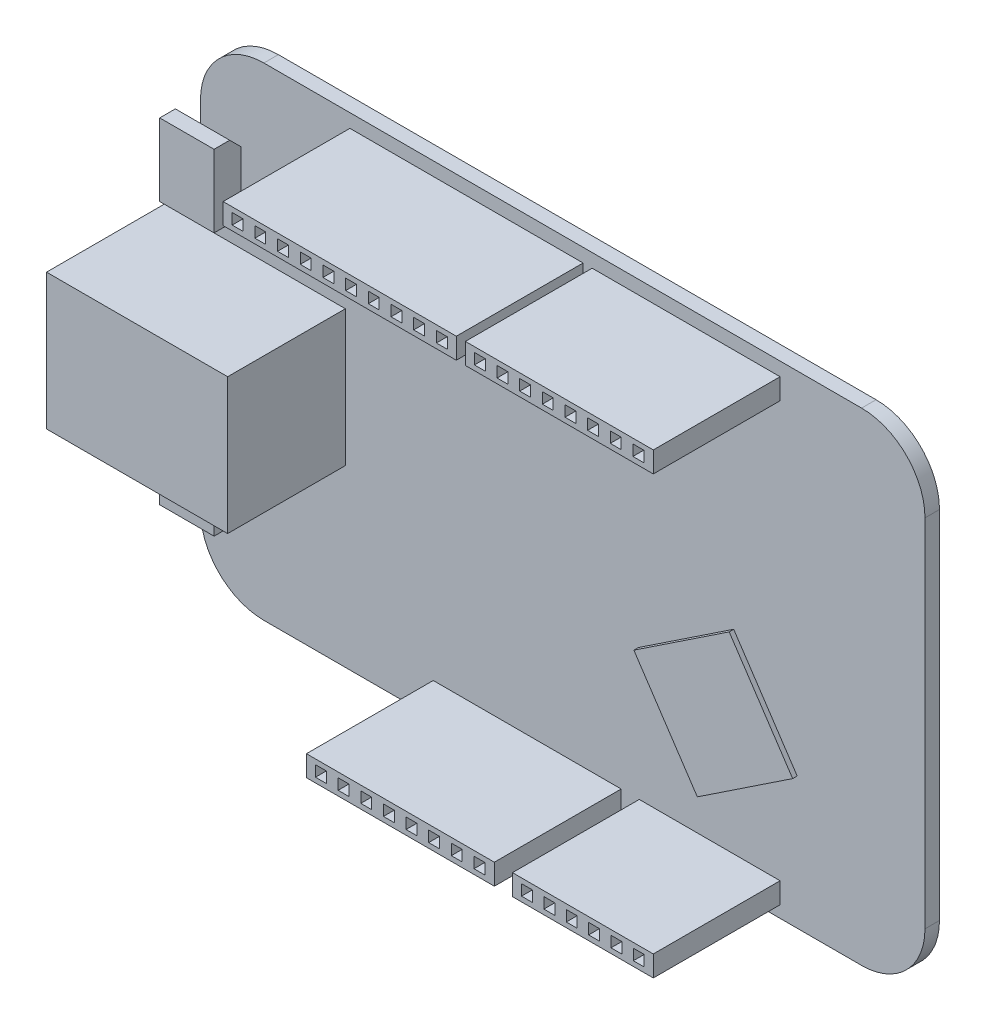
SolidWorks part; units mm, degrees
other "Camera1"
ref_plane "Plan de face" through (0, 0, 0) normal (0, 0, 1) x (1, 0, 0)
ref_plane "Plan de dessus" through (0, 0, 0) normal (0, 1, 0) x (1, 0, 0)
ref_plane "Plan de droite" through (0, 0, 0) normal (1, 0, 0) x (0, 0, -1)
sketch "Esquisse1" plane through (0, 0, 0) normal (0, 0, 1) x (1, 0, 0)
  line L0 (0, 0) -> (0, 53.3)
  line L1 (0, 53.3) -> (80, 53.3)
  line L2 (80, 53.3) -> (80, 0)
  line L6 (80, 0) -> (0, 0)
  dimension "D1" = 53.3
  dimension "D2" = 80
extrude "Boss.-Extru.1" add sketch "Esquisse1" along normal blind 1.6
sketch "Esquisse4" plane through (0, 0, 1.6) normal (0, 0, 1) x (1, 0, 0)
  line L0 (0, 0) -> (80, 0) construction
  line L1 (64, 3.6) -> (48.45, 3.6)
  line L2 (64, 3.6) -> (64, 1.3)
  line L3 (64, 1.3) -> (48.45, 1.3)
  line L4 (48.45, 3.6) -> (48.45, 1.3)
  line L5 (49.45, 3.05) -> (50.65, 3.05)
  line L6 (49.45, 3.05) -> (49.45, 1.85)
  line L7 (49.45, 1.85) -> (50.65, 1.85)
  line L8 (50.65, 3.05) -> (50.65, 1.85)
  line L10 (51.92, 1.85) -> (53.12, 1.85)
  line L11 (53.12, 3.05) -> (53.12, 1.85)
  line L12 (51.92, 3.05) -> (53.12, 3.05)
  line L13 (51.92, 3.05) -> (51.92, 1.85)
  line L14 (54.39, 1.85) -> (55.59, 1.85)
  line L15 (55.59, 3.05) -> (55.59, 1.85)
  line L16 (54.39, 3.05) -> (55.59, 3.05)
  line L17 (54.39, 3.05) -> (54.39, 1.85)
  line L18 (56.86, 1.85) -> (58.06, 1.85)
  line L19 (58.06, 3.05) -> (58.06, 1.85)
  line L20 (56.86, 3.05) -> (58.06, 3.05)
  line L21 (56.86, 3.05) -> (56.86, 1.85)
  line L22 (59.33, 1.85) -> (60.53, 1.85)
  line L23 (60.53, 3.05) -> (60.53, 1.85)
  line L24 (59.33, 3.05) -> (60.53, 3.05)
  line L25 (59.33, 3.05) -> (59.33, 1.85)
  line L26 (61.8, 1.85) -> (63, 1.85)
  line L27 (63, 3.05) -> (63, 1.85)
  line L28 (61.8, 3.05) -> (63, 3.05)
  line L29 (61.8, 3.05) -> (61.8, 1.85)
  line L30 (80, 0) -> (80, 53.3) construction
  dimension "D1" = 1
  dimension "D2" = 2.3
  dimension "D3" = 1.3
  dimension "D4" = 16
  dimension "D5" = 1.2
  dimension "D6" = 0.55
  dimension "D7" = 1
  dimension "D9" = 15.55
  dimension "D8" = 6
extrude "Boss.-Extru.4" add sketch "Esquisse4" along normal blind 14 separate body
sketch "Esquisse8" plane through (0, 0, 1.6) normal (0, 0, 1) x (1, 0, 0)
  line L0 (64, 3.6) -> (48.45, 3.6) construction
  line L1 (46.45, 3.6) -> (25.7, 3.6)
  line L2 (46.45, 3.6) -> (46.45, 1.3)
  line L3 (46.45, 1.3) -> (25.7, 1.3)
  line L4 (25.7, 3.6) -> (25.7, 1.3)
  line L5 (48.45, 1.3) -> (64, 1.3) construction
  line L6 (48.45, 3.6) -> (48.45, 1.3) construction
  line L7 (50.65, 3.05) -> (49.45, 3.05) construction
  line L8 (26.7, 3.05) -> (27.9, 3.05)
  line L9 (26.7, 3.05) -> (26.7, 1.85)
  line L10 (26.7, 1.85) -> (27.9, 1.85)
  line L11 (27.9, 3.05) -> (27.9, 1.85)
  line L12 (49.45, 1.85) -> (50.65, 1.85) construction
  line L13 (29.2, 1.85) -> (30.4, 1.85)
  line L14 (30.4, 3.05) -> (30.4, 1.85)
  line L15 (29.2, 3.05) -> (30.4, 3.05)
  line L16 (29.2, 3.05) -> (29.2, 1.85)
  line L17 (31.7, 1.85) -> (32.9, 1.85)
  line L18 (32.9, 3.05) -> (32.9, 1.85)
  line L19 (31.7, 3.05) -> (32.9, 3.05)
  line L20 (31.7, 3.05) -> (31.7, 1.85)
  line L21 (34.2, 1.85) -> (35.4, 1.85)
  line L22 (35.4, 3.05) -> (35.4, 1.85)
  line L23 (34.2, 3.05) -> (35.4, 3.05)
  line L24 (34.2, 3.05) -> (34.2, 1.85)
  line L25 (36.7, 1.85) -> (37.9, 1.85)
  line L26 (37.9, 3.05) -> (37.9, 1.85)
  line L27 (36.7, 3.05) -> (37.9, 3.05)
  line L28 (36.7, 3.05) -> (36.7, 1.85)
  line L29 (39.2, 1.85) -> (40.4, 1.85)
  line L30 (40.4, 3.05) -> (40.4, 1.85)
  line L31 (39.2, 3.05) -> (40.4, 3.05)
  line L32 (39.2, 3.05) -> (39.2, 1.85)
  line L33 (41.7, 1.85) -> (42.9, 1.85)
  line L34 (42.9, 3.05) -> (42.9, 1.85)
  line L35 (41.7, 3.05) -> (42.9, 3.05)
  line L36 (41.7, 3.05) -> (41.7, 1.85)
  line L37 (44.2, 1.85) -> (45.4, 1.85)
  line L38 (45.4, 3.05) -> (45.4, 1.85)
  line L39 (44.2, 3.05) -> (45.4, 3.05)
  line L40 (44.2, 3.05) -> (44.2, 1.85)
  point P8 (48.45, 2.45)
  dimension "D1" = 2
  dimension "D2" = 20.75
  dimension "D3" = 1.2
  dimension "D4" = 1
  dimension "D5" = 8
extrude "Boss.-Extru.6" add sketch "Esquisse8" along normal blind 14 separate body
sketch "Esquisse19" plane through (0, 0, 1.6) normal (0, 0, 1) x (1, 0, 0)
  line L0 (64, 51.8) -> (43.25, 51.8)
  line L1 (64, 51.8) -> (64, 49.5)
  line L2 (64, 49.5) -> (43.25, 49.5)
  line L3 (43.25, 51.8) -> (43.25, 49.5)
  line L4 (44.25, 51.25) -> (45.45, 51.25)
  line L5 (44.25, 51.25) -> (44.25, 50.05)
  line L6 (44.25, 50.05) -> (45.45, 50.05)
  line L7 (45.45, 51.25) -> (45.45, 50.05)
  line L8 (46.75, 50.05) -> (47.95, 50.05)
  line L9 (47.95, 51.25) -> (47.95, 50.05)
  line L10 (46.75, 51.25) -> (47.95, 51.25)
  line L11 (46.75, 51.25) -> (46.75, 50.05)
  line L12 (49.25, 50.05) -> (50.45, 50.05)
  line L13 (50.45, 51.25) -> (50.45, 50.05)
  line L14 (49.25, 51.25) -> (50.45, 51.25)
  line L15 (49.25, 51.25) -> (49.25, 50.05)
  line L16 (51.75, 50.05) -> (52.95, 50.05)
  line L17 (52.95, 51.25) -> (52.95, 50.05)
  line L18 (51.75, 51.25) -> (52.95, 51.25)
  line L19 (51.75, 51.25) -> (51.75, 50.05)
  line L20 (54.25, 50.05) -> (55.45, 50.05)
  line L21 (55.45, 51.25) -> (55.45, 50.05)
  line L22 (54.25, 51.25) -> (55.45, 51.25)
  line L23 (54.25, 51.25) -> (54.25, 50.05)
  line L24 (56.75, 50.05) -> (57.95, 50.05)
  line L25 (57.95, 51.25) -> (57.95, 50.05)
  line L26 (56.75, 51.25) -> (57.95, 51.25)
  line L27 (56.75, 51.25) -> (56.75, 50.05)
  line L28 (59.25, 50.05) -> (60.45, 50.05)
  line L29 (60.45, 51.25) -> (60.45, 50.05)
  line L30 (59.25, 51.25) -> (60.45, 51.25)
  line L31 (59.25, 51.25) -> (59.25, 50.05)
  line L32 (61.75, 50.05) -> (62.95, 50.05)
  line L33 (62.95, 51.25) -> (62.95, 50.05)
  line L34 (61.75, 51.25) -> (62.95, 51.25)
  line L35 (61.75, 51.25) -> (61.75, 50.05)
  line L36 (80, 0) -> (80, 53.3) construction
  line L38 (80, 53.3) -> (0, 53.3) construction
  dimension "D1" = 20.75
  dimension "D2" = 1.2
  dimension "D3" = 1
  dimension "D4" = 2.3
  dimension "D5" = 0.55
  dimension "D6" = 0.55
  dimension "D7" = 1.2
  dimension "D8" = 1.3
  dimension "D9" = 1.3
  dimension "D10" = 1.3
  dimension "D11" = 1.3
  dimension "D12" = 1.3
  dimension "D13" = 1.3
  dimension "D14" = 1.3
  dimension "D15" = 1.05
  dimension "D16" = 1.2
  dimension "D17" = 1.2
  dimension "D18" = 1.2
  dimension "D19" = 1.2
  dimension "D20" = 1.2
  dimension "D21" = 1.2
  dimension "D22" = 16
  dimension "D23" = 1.5
extrude "Boss.-Extru.15" add sketch "Esquisse19" along normal blind 14 separate body
sketch "Esquisse20" plane through (0, 0, 1.6) normal (0, 0, 1) x (1, 0, 0)
  line L0 (43.25, 49.5) -> (64, 49.5) construction
  line L1 (42.25, 49.5) -> (16.5, 49.5)
  line L2 (42.25, 49.5) -> (42.25, 51.8)
  line L3 (42.25, 51.8) -> (16.5, 51.8)
  line L4 (16.5, 49.5) -> (16.5, 51.8)
  line L5 (64, 51.8) -> (43.25, 51.8) construction
  line L6 (43.25, 51.8) -> (43.25, 49.5) construction
  line L7 (45.45, 51.25) -> (44.25, 51.25) construction
  line L8 (41.25, 50.05) -> (40.05, 50.05)
  line L9 (41.25, 50.05) -> (41.25, 51.25)
  line L10 (41.25, 51.25) -> (40.05, 51.25)
  line L11 (40.05, 50.05) -> (40.05, 51.25)
  line L12 (44.25, 50.05) -> (45.45, 50.05) construction
  line L13 (38.7444, 50.05) -> (37.5444, 50.05)
  line L14 (37.5444, 50.05) -> (37.5444, 51.25)
  line L15 (38.7444, 51.25) -> (37.5444, 51.25)
  line L16 (38.7444, 50.05) -> (38.7444, 51.25)
  line L17 (36.2389, 50.05) -> (35.0389, 50.05)
  line L18 (35.0389, 50.05) -> (35.0389, 51.25)
  line L19 (36.2389, 51.25) -> (35.0389, 51.25)
  line L20 (36.2389, 50.05) -> (36.2389, 51.25)
  line L21 (33.7333, 50.05) -> (32.5333, 50.05)
  line L22 (32.5333, 50.05) -> (32.5333, 51.25)
  line L23 (33.7333, 51.25) -> (32.5333, 51.25)
  line L24 (33.7333, 50.05) -> (33.7333, 51.25)
  line L25 (31.2278, 50.05) -> (30.0278, 50.05)
  line L26 (30.0278, 50.05) -> (30.0278, 51.25)
  line L27 (31.2278, 51.25) -> (30.0278, 51.25)
  line L28 (31.2278, 50.05) -> (31.2278, 51.25)
  line L29 (28.7222, 50.05) -> (27.5222, 50.05)
  line L30 (27.5222, 50.05) -> (27.5222, 51.25)
  line L31 (28.7222, 51.25) -> (27.5222, 51.25)
  line L32 (28.7222, 50.05) -> (28.7222, 51.25)
  line L33 (26.2167, 50.05) -> (25.0167, 50.05)
  line L34 (25.0167, 50.05) -> (25.0167, 51.25)
  line L35 (26.2167, 51.25) -> (25.0167, 51.25)
  line L36 (26.2167, 50.05) -> (26.2167, 51.25)
  line L37 (23.7111, 50.05) -> (22.5111, 50.05)
  line L38 (22.5111, 50.05) -> (22.5111, 51.25)
  line L39 (23.7111, 51.25) -> (22.5111, 51.25)
  line L40 (23.7111, 50.05) -> (23.7111, 51.25)
  line L41 (21.2056, 50.05) -> (20.0056, 50.05)
  line L42 (20.0056, 50.05) -> (20.0056, 51.25)
  line L43 (21.2056, 51.25) -> (20.0056, 51.25)
  line L44 (21.2056, 50.05) -> (21.2056, 51.25)
  line L45 (18.7, 50.05) -> (17.5, 50.05)
  line L46 (17.5, 50.05) -> (17.5, 51.25)
  line L47 (18.7, 51.25) -> (17.5, 51.25)
  line L48 (18.7, 50.05) -> (18.7, 51.25)
  dimension "D1" = 25.75
  dimension "D2" = 1
  dimension "D3" = 1.2
  dimension "D4" = 1
  dimension "D6" = 1
  dimension "D5" = 10
extrude "Boss.-Extru.16" add sketch "Esquisse20" along normal blind 14 separate body
fillet "Fillet1" radius 7 4 edges at (80, 53.3, 0.8) (80, 0, 0.8) (0, 0, 0.8) (0, 53.3, 0.8)
sketch "Sketch1" plane through (0, 0, 1.6) normal (0, 0, 1) x (1, 0, 0)
  line L0 (55.3626, 7.5515) -> (65.8884, 14.561)
  line L1 (65.8884, 14.561) -> (58.8788, 25.0868)
  line L2 (58.8788, 25.0868) -> (48.353, 18.0772)
  line L3 (48.353, 18.0772) -> (55.3626, 7.5515)
extrude "Boss-Extrude1" add sketch "Sketch1" along normal blind 0.5
sketch "Sketch2" plane through (0, 0, 1.6) normal (0, 0, 1) x (1, 0, 0)
  line L0 (73, 53.3) -> (7, 53.3) construction
  line L1 (-4, 19.3) -> (16, 19.3)
  line L2 (-4, 19.3) -> (-4, 34.3)
  line L3 (-4, 34.3) -> (16, 34.3)
  line L4 (16, 19.3) -> (16, 34.3)
  line L5 (0, 46.3) -> (0, 7) construction
  dimension "D1" = 20
  dimension "D2" = 15
  dimension "D3" = 19
  dimension "D4" = 4
extrude "Boss-Extrude2" add sketch "Sketch2" along normal blind 13
sketch "Sketch3" plane through (0, 0, 1.6) normal (0, 0, 1) x (1, 0, 0)
  line L0 (-4, 19.3) -> (16, 19.3) construction
  line L1 (4.5, 45.3) -> (-1.5, 45.3)
  line L2 (4.5, 45.3) -> (4.5, 37.3)
  line L3 (4.5, 37.3) -> (-1.5, 37.3)
  line L4 (-1.5, 45.3) -> (-1.5, 37.3)
  line L5 (4.5, 16.3) -> (-1.5, 16.3)
  line L6 (4.5, 16.3) -> (4.5, 8.3)
  line L7 (4.5, 8.3) -> (-1.5, 8.3)
  line L8 (-1.5, 16.3) -> (-1.5, 8.3)
  line L9 (16, 34.3) -> (0, 34.3) construction
  line L10 (0, 19.3) -> (0, 7) construction
  line L11 (0, 46.3) -> (0, 34.3) construction
  dimension "D1" = 3
  dimension "D2" = 3
  dimension "D3" = 8
  dimension "D4" = 6
  dimension "D5" = 1.5
  dimension "D6" = 8
  dimension "D7" = 6
  dimension "D8" = 1.5
extrude "Boss-Extrude3" add sketch "Sketch3" along normal blind 3
sketch "Sketch4" plane through (-1.5, 0, 0) normal (-1, 0, 0) x (0, 0, 1)
  line L0 (2.873, 8.3) -> (1.6, 9.5726)
  line L1 (4.6, 8.3) -> (1.6, 8.3) construction
  line L2 (1.6, 16.3) -> (1.6, 8.3) construction
  line L3 (1.6, 9.5726) -> (1.6, 8.3)
  line L4 (1.6, 8.3) -> (2.873, 8.3)
  line L5 (2.873, 16.3) -> (1.6, 16.3)
  line L6 (4.6, 16.3) -> (1.6, 16.3) construction
  line L7 (1.6, 16.3) -> (1.6, 15.0274)
  line L8 (1.6, 16.3) -> (1.6, 8.3) construction
  line L9 (1.6, 15.0274) -> (2.873, 16.3)
  line L10 (2.8733, 37.3) -> (1.6, 38.573)
  line L11 (4.6, 37.3) -> (1.6, 37.3) construction
  line L12 (1.6, 45.3) -> (1.6, 37.3) construction
  line L13 (1.6, 38.573) -> (1.6, 37.3)
  line L14 (1.6, 37.3) -> (2.8733, 37.3)
  line L15 (2.8726, 45.3) -> (1.6, 44.027)
  line L16 (4.6, 45.3) -> (1.6, 45.3) construction
  line L17 (1.6, 44.027) -> (1.6, 45.3)
  line L18 (1.6, 45.3) -> (2.8726, 45.3)
  dimension "D1" = 1.8
  dimension "D2" = 1.8005
  dimension "D3" = 1.8
  dimension "D4" = 1.8
extrude "Cut-Extrude1" cut sketch "Sketch4" against normal up to next (6 mm away)
sketch "Sketch5" plane through (-4, 0, 0) normal (-1, 0, 0) x (0, 0, 1)
  line L0 (14.6, 34.3) -> (14.6, 19.3) construction
  line L1 (13.6, 33.3) -> (3.6, 33.3)
  line L2 (13.6, 33.3) -> (13.6, 20.3)
  line L3 (13.6, 20.3) -> (3.6, 20.3)
  line L4 (3.6, 33.3) -> (3.6, 30.3)
  line L5 (14.6, 19.3) -> (1.6, 19.3) construction
  line L6 (14.6, 34.3) -> (1.6, 34.3) construction
  line L7 (1.6, 34.3) -> (1.6, 19.3) construction
  line L8 (3.6, 30.3) -> (2.6, 30.3)
  line L9 (2.6, 30.3) -> (2.6, 23.3)
  line L10 (2.6, 23.3) -> (3.6, 23.3)
  line L11 (3.6, 23.3) -> (3.6, 20.3)
  line L12 (1.6, 34.3) -> (1.6, 19.3) construction
  dimension "D1" = 1
  dimension "D2" = 1
  dimension "D3" = 1
  dimension "D4" = 2
  dimension "D5" = 1
  dimension "D6" = 3
  dimension "D7" = 3
extrude "Cut-Extrude2" cut sketch "Sketch5" against normal blind 18
